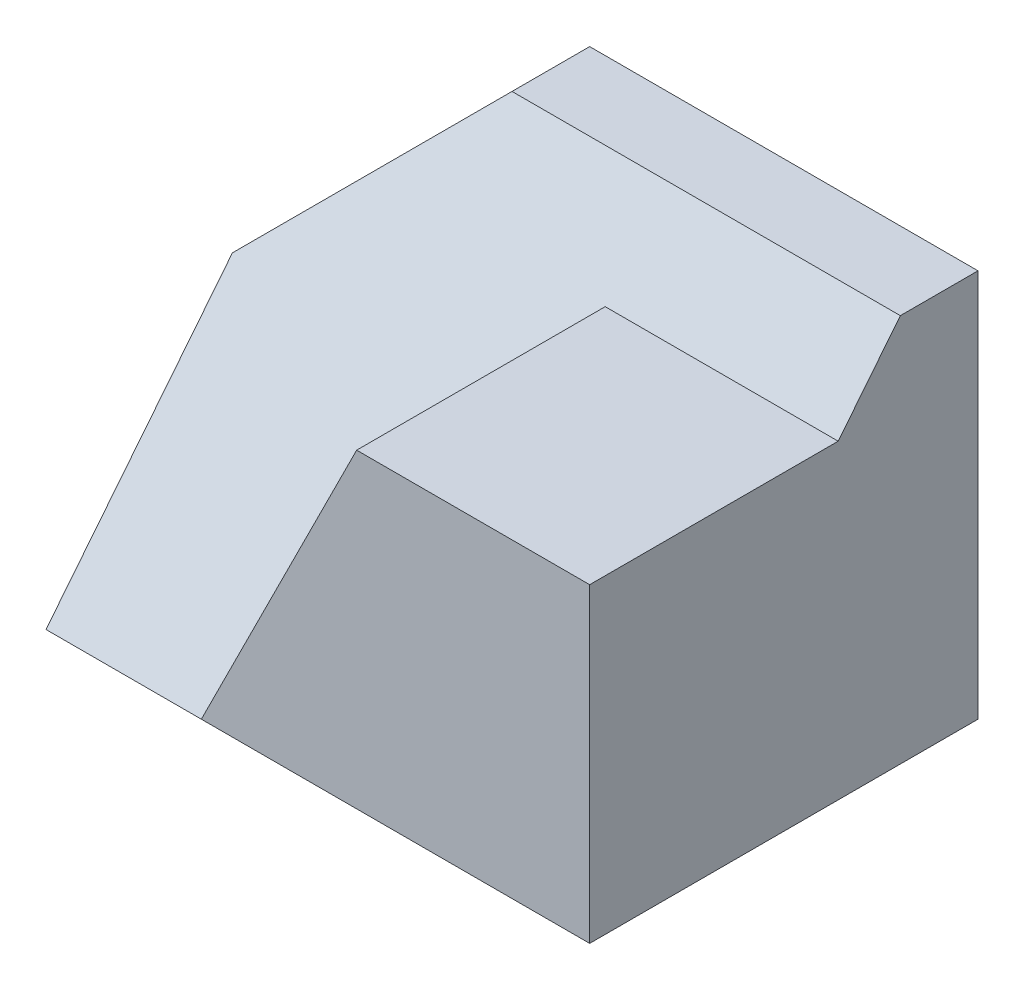
SolidWorks part; units mm, degrees
ref_plane "Front Plane" through (0, 0, 0) normal (0, 0, 1) x (1, 0, 0)
ref_plane "Top Plane" through (0, 0, 0) normal (0, 1, 0) x (1, 0, 0)
ref_plane "Right Plane" through (0, 0, 0) normal (1, 0, 0) x (0, 0, -1)
sketch "Sketch1" plane through (0, 0, 0) normal (0, 0, 1) x (1, 0, 0)
  line L1 (0, 0) -> (70, 0)
  line L2 (0, 0) -> (0, 50)
  line L3 (0, 50) -> (70, 50)
  line L4 (70, 0) -> (70, 50)
  dimension "D1" = 70
  dimension "D2" = 50
extrude "Boss-Extrude1" add sketch "Sketch1" along normal blind 50
sketch "Sketch2" plane through (0, 0, 50) normal (0, 0, 1) x (1, 0, 0)
  line L0 (20, 50) -> (0, 30)
  line L1 (70, 50) -> (0, 50) construction
  line L2 (0, 50) -> (0, 0) construction
  line L3 (0, 30) -> (0, 50)
  line L4 (0, 50) -> (20, 50)
  dimension "D1" = 20
  dimension "D2" = 20
extrude "Cut-Extrude1" cut sketch "Sketch2" against normal blind 50
sketch "Sketch3" plane through (70, 0, 0) normal (1, 0, 0) x (0, 0, -1)
  line L0 (-50, 40) -> (-20, 40)
  line L1 (-50, 0) -> (-50, 50) construction
  line L2 (-20, 40) -> (-10, 50)
  line L3 (-50, 50) -> (0, 50) construction
  line L4 (-10, 50) -> (-50, 50)
  line L5 (-50, 50) -> (-50, 40)
  dimension "D1" = 10
  dimension "D2" = 40
  dimension "D3" = 30
extrude "Cut-Extrude2" cut sketch "Sketch3" against normal blind 81
sketch "Sketch4" plane through (0, 0, 50) normal (0, 0, 1) x (1, 0, 0)
  line L0 (20, 0) -> (70, 0)
  line L1 (0, 0) -> (70, 0) construction
  line L2 (70, 0) -> (70, 40)
  line L3 (70, 40) -> (40, 40)
  line L4 (10, 40) -> (70, 40) construction
  line L5 (40, 40) -> (20, 0)
  line L6 (40, 40) -> (10, 40)
  line L7 (10, 40) -> (0, 30)
  line L8 (0, 30) -> (0, 0)
  line L9 (0, 0) -> (20, 0)
  line M6 (70, 40) -> (10, 40)
  line M7 (10, 40) -> (0, 30)
  line M8 (0, 30) -> (0, 0)
  line M9 (0, 0) -> (70, 0)
  dimension "D1" = 20
  dimension "D2" = 30
extrude "Cut-Extrude4" cut sketch "Sketch4" against normal blind 30 contours L5 M6 M7 M8 M9
ref_plane "Plane1" through (0, 24, 32) normal (0, 0.6, 0.8) x (1, 0, 0)
ref_plane "Plane2" through (0, 24.3902, 30.4878) normal (0, -0.6247, -0.7809) x (-1, 0, 0)
sketch "Sketch5" plane through (0, 0, 50) normal (0, 0, 1) x (1, 0, 0)
  point P0 (20, 0)
  point P1 (0, 0)
ref_plane "Plane3" through (0, 24.3902, 30.4878) normal (0, 0.6247, 0.7809) x (1, 0, 0)
sketch "Sketch6" plane through (0, 24.3902, 30.4878) normal (0, 0.6247, 0.7809) x (1, 0, 0)
  line L0 (0, -31.2348) -> (20, -31.2348)
  line L1 (20, -31.2348) -> (20, 32.7965)
  line L2 (20, 32.7965) -> (0, -31.2348)
  line L3 (20, -31.2348) -> (70, 32.7965)
  line L4 (70, 32.7965) -> (20, 32.7965)
extrude "Boss-Extrude4" add sketch "Sketch6" against normal blind 73 contours L3 L4 L1 | L1 L2 L0
sketch "Sketch7" plane through (0, 0, 0) normal (0, -1, 0) x (1, 0, 0)
  line L1 (70, 50) -> (0, 50)
  line L2 (70, 50) -> (70, 0)
  line L3 (70, 0) -> (0, 0)
  line L4 (0, 50) -> (0, 0)
extrude "Cut-Extrude5" cut sketch "Sketch7" along normal blind 73
sketch "Sketch8" plane through (0, 0, 0) normal (0, 0, -1) x (-1, 0, 0)
  line L1 (-70, 50) -> (0, 50)
  line L2 (-70, 50) -> (-70, 0)
  line L3 (-70, 0) -> (0, 0)
  line L4 (0, 50) -> (0, 0)
extrude "Cut-Extrude6" cut sketch "Sketch8" along normal blind 73
sketch "Sketch9" plane through (0, 0, 0) normal (0, 0, 1) x (1, 0, 0)
  line L0 (9.7561, 0) -> (0, -40)
  line L1 (0, -40) -> (20, -40)
  line L2 (20, -40) -> (44.3902, 0)
  line L3 (44.3902, 0) -> (9.7561, 0)
extrude "Cut-Extrude7" cut sketch "Sketch9" against normal blind 73
sketch "Sketch10" plane through (32.3591, -19.7311, 0) normal (-0.8538, 0.5206, 0) x (0, 0, 1)
  line L0 (0, 23.1099) -> (0, -23.7397)
  line L1 (0, -23.7397) -> (-11.4856, -23.7397)
  line L2 (-11.4856, -23.7397) -> (-43.4856, 23.1099)
  line L3 (-43.4856, 23.1099) -> (0, 23.1099)
extrude "Cut-Extrude8" cut sketch "Sketch10" against normal blind 73
sketch "Sketch11" plane through (0, 24.3902, 30.4878) normal (0, 0.6247, 0.7809) x (1, 0, 0)
  line L0 (0, -31.2348) -> (20, -31.2348)
  line L1 (20, -31.2348) -> (70, 32.7965)
  line L2 (70, 32.7965) -> (20, 32.7965)
  line L3 (20, 32.7965) -> (0, 4.6852)
  line L4 (0, 4.6852) -> (0, -31.2348)
  line L7 (10, 18.7409) -> (20, 32.7965) construction
extrude "Cut-Extrude9" cut sketch "Sketch11" along normal blind 73
sketch "Sketch12" plane through (-2.2131, 1.2295, -0.9836) normal (0.8148, -0.4527, 0.3621) x (0.3166, -0.1759, -0.9321)
  line L0 (-22.5116, 36.9628) -> (-11.7834, 53.4207)
  line L1 (-11.7834, 53.4207) -> (-22.5116, 39.8227)
  line L2 (-22.5116, 39.8227) -> (-22.5116, 36.9628)
extrude "Cut-Extrude10" cut sketch "Sketch12" against normal blind 73
sketch "Sketch13" plane through (-7.1265, 3.9592, 20.9836) normal (0.3166, -0.1759, -0.9321) x (-0.9486, -0.0587, -0.3111)
  line L0 (-18.0551, 35.5983) -> (-15.8379, 33.5905)
  line L1 (-15.8379, 33.5905) -> (-16.5909, 33.1417)
  line L2 (-16.5909, 33.1417) -> (-18.0551, 35.5983)
extrude "Cut-Extrude11" cut sketch "Sketch13" against normal blind 73
sketch "Sketch14" plane through (17.9507, 32.3113, 0) normal (0.4856, 0.8742, 0) x (0.8742, -0.4856, 0)
  line L0 (-11.5013, -19.6825) -> (-10.6841, -20)
  line L1 (-10.6841, -20) -> (-11.5013, -20)
  line L2 (-11.5013, -20) -> (-11.5013, -19.6825)
extrude "Cut-Extrude12" cut sketch "Sketch14" against normal blind 73
sketch "Sketch15" plane through (0, 0, 0) normal (0, 1, 0) x (1, 0, 0)
  line L0 (44.3902, 43.4856) -> (44.3902, 0)
  line L1 (44.3902, 0) -> (65.6027, 43.4856)
  line L2 (65.6027, 43.4856) -> (44.3902, 43.4856)
extrude "Cut-Extrude13" cut sketch "Sketch15" against normal blind 73
sketch "Sketch16" plane through (0, -40, 0) normal (0, 1, 0) x (1, 0, 0)
  line L0 (20, 11.4856) -> (20, 0)
  line L1 (20, 0) -> (0, 0)
  line L2 (0, 0) -> (2.2411, 11.4856)
  line L3 (2.2411, 11.4856) -> (20, 11.4856)
extrude "Cut-Extrude14" cut sketch "Sketch16" against normal blind 73
sketch "Sketch17" plane through (0, 0, 0) normal (0.9815, 0, 0.1915) x (0.1915, 0, -0.9815)
  line L0 (11.7022, -40) -> (7.1355, -45.6027)
  line L1 (7.1355, -45.6027) -> (0, -40)
  line L2 (0, -40) -> (11.7022, -40)
extrude "Cut-Extrude15" cut sketch "Sketch17" against normal blind 73
sketch "Sketch18" plane through (20, 0, 0) normal (-1, 0, 0) x (0, 0, 1)
  line L0 (-7.0034, -45.6027) -> (0, -40)
  line L1 (0, -40) -> (-11.4856, -40)
  line L2 (-11.4856, -40) -> (-7.0034, -45.6027)
extrude "Cut-Extrude16" cut sketch "Sketch18" against normal blind 73
sketch "Sketch19" plane through (0, -24.3902, 19.5122) normal (0, -0.7809, 0.6247) x (1, 0, 0)
  line L0 (0, -33.9566) -> (1.3665, -33.9566)
  line L1 (1.3665, -33.9566) -> (0, -24.9878)
  line L2 (0, -24.9878) -> (0, -33.9566)
extrude "Cut-Extrude17" cut sketch "Sketch19" against normal blind 73
sketch "Sketch20" plane through (0, 0, 50) normal (0, 0, 1) x (1, 0, 0)
  line L0 (20, 0) -> (70, 0)
  line L1 (70, 0) -> (70, 40)
  line L2 (70, 40) -> (40, 40)
  line L3 (40, 40) -> (20, 0)
  dimension "D1" = 30
extrude "Boss-Extrude6" add sketch "Sketch20" against normal blind 40
ref_plane "Plane4" through (-11.1111, 22.2222, 22.2222) normal (-0.3333, 0.6667, 0.6667) x (0.9428, 0.2357, 0.2357)
sketch "Sketch22" plane through (0, 0, 0) normal (-1, 0, 0) x (0, 0, 1)
  line L0 (20, 0) -> (50, 0)
  line L1 (50, 0) -> (20, 50)
  line L2 (20, 50) -> (20, 0)
  dimension "D1" = 50
extrude "Boss-Extrude9" add sketch "Sketch22" against normal blind 20
sketch "Sketch23" plane through (0, 24.3902, 30.4878) normal (0, 0.6247, 0.7809) x (1, 0, 0)
  line L0 (20, 32.7965) -> (20, -31.2348)
  line L1 (20, -31.2348) -> (0, -31.2348)
  line L2 (0, -31.2348) -> (20, 32.7965)
  line L3 (0, -31.2348) -> (0, 0)
  line L4 (0, 0) -> (20, 32.7965)
  line L5 (0, 0) -> (20, 32.7965)
extrude "Cut-Extrude18" cut sketch "Sketch23" along normal blind 20 contours L2 L1 L0
sketch "Sketch24" plane through (0, 24.3902, 30.4878) normal (0, 0.6247, 0.7809) x (1, 0, 0)
  line L0 (20, 32.7965) -> (20, -31.2348)
  line L1 (20, -31.2348) -> (0, -31.2348)
  line L2 (0, -31.2348) -> (0, 0)
  line L3 (0, 0) -> (20, 32.7965)
extrude "Cut-Extrude19" cut sketch "Sketch24" along normal blind 20
sketch "Sketch25" plane through (0, 0, 0) normal (0.8538, -0.4066, 0.3252) x (0.2937, -0.1398, -0.9456)
  line L0 (-35.7262, 24.4016) -> (-32.2408, 22.021)
  line L1 (-32.2408, 22.021) -> (-21.1499, 38.259)
  line L2 (-21.1499, 38.259) -> (-21.1499, 52.1039)
  line L3 (-21.1499, 52.1039) -> (-35.7262, 24.4016)
extrude "Cut-Extrude20" cut sketch "Sketch25" against normal blind 20
sketch "Sketch26" plane through (0, 0, 20) normal (0, 0, -1) x (-1, 0, 0)
  line L0 (0, 30) -> (0, 37.5)
  line L1 (0, 37.5) -> (-7.5, 37.5)
  line L2 (-7.5, 37.5) -> (0, 30)
extrude "Cut-Extrude21" cut sketch "Sketch26" against normal blind 20
sketch "Sketch27" plane through (-2.5647, 23.3879, 35.9673) normal (0.0597, -0.5442, -0.8369) x (-0.9982, -0.0325, -0.05)
  line L0 (-2.5693, 16.7336) -> (-2.5693, 29.5261)
  line L1 (-2.5693, 29.5261) -> (-18.7887, 31.0145)
  line L2 (-18.7887, 31.0145) -> (-9.9634, 16.4467)
  line L3 (-9.9634, 16.4467) -> (-2.5693, 16.7336)
extrude "Cut-Extrude22" cut sketch "Sketch27" against normal blind 20
sketch "Sketch28" plane through (0, 0, 0) normal (-1, 0, 0) x (0, 0, 1)
  line L0 (50, 0) -> (0, 0) construction
  line L1 (0, 30) -> (25, 30)
  line L2 (0, 30) -> (0, 0)
  line L3 (0, 0) -> (25, 0)
  line L4 (25, 30) -> (25, 0)
extrude "Boss-Extrude10" add sketch "Sketch28" against normal blind 20
sketch "Sketch29" plane through (0, 0, 20) normal (0, 0, -1) x (-1, 0, 0)
  line L0 (0, 48.2245) -> (0, 50)
  line L1 (0, 50) -> (-16.1905, 50)
  line L2 (0, 48.2245) -> (-16.1905, 50) construction
  line L3 (-16.1905, 50) -> (0, 48.2245)
extrude "Cut-Extrude23" cut sketch "Sketch29" against normal blind 20
sketch "Sketch30" plane through (0, 24.3902, 30.4878) normal (0, 0.6247, 0.7809) x (1, 0, 0)
  line L0 (20, 32.7965) -> (0, 7.184)
  line L1 (0, 7.184) -> (19.3918, 9.5701)
  line L2 (19.3918, 9.5701) -> (20, 32.7965)
  dimension "D1" = 19.3918
  dimension "D2" = 23.2264
extrude "Boss-Extrude12" add sketch "Sketch30" against normal blind 10
sketch "Sketch31" plane through (-2.5647, 23.3879, 35.9673) normal (0.0597, -0.5442, -0.8369) x (-0.9982, -0.0325, -0.05)
  line L0 (-9.6788, 15.9767) -> (-2.5693, 7.7874)
  line L1 (-2.5693, 7.7874) -> (-2.5693, 4.2412)
  line L2 (-2.5693, 4.2412) -> (-9.6788, 15.9767)
extrude "Cut-Extrude24" cut sketch "Sketch31" against normal blind 10
sketch "Sketch32" plane through (0, 37.5, 0) normal (0, -1, 0) x (-1, 0, 0)
  line L0 (-7.381, -27.5) -> (0, -26.9737)
  line L1 (0, -26.9737) -> (0, -27.5)
  line L2 (0, -27.5) -> (-7.381, -27.5)
extrude "Cut-Extrude25" cut sketch "Sketch32" against normal blind 10
ref_plane "Plane6" through (0, 24.3902, 30.4878) normal (0, 0.6247, 0.7809) x (1, 0, 0)
sketch "Sketch35" plane through (0, 24.3902, 30.4878) normal (0, 0.6247, 0.7809) x (1, 0, 0)
  line L0 (70, 32.7965) -> (70, -31.2348)
  line L1 (70, -31.2348) -> (0, -31.2348)
  line L2 (0, -31.2348) -> (70, 32.7965)
extrude "Cut-Extrude28" cut sketch "Sketch35" along normal blind 10
sketch "Sketch36" plane through (0, 0, 50) normal (0, 0, 1) x (1, 0, 0)
  line L0 (70, 16.0078) -> (70, 0)
  line L1 (70, 0) -> (20, 0)
  line L2 (20, 0) -> (40, 40)
  line L3 (40, 40) -> (70, 40)
  line L4 (70, 40) -> (70, 0)
  line L5 (70, 0) -> (70.0012, 0.4952)
  line M1 (28.0039, 16.0078) -> (70, 16.0078)
  line M2 (70, 16.0078) -> (70, 40)
  line M3 (70, 40) -> (40, 40)
  line M4 (40, 40) -> (28.0039, 16.0078)
extrude "Boss-Extrude14" add sketch "Sketch36" against normal blind 35 contours L2 L1 L0 M1 | M4 M1 M2 M3
